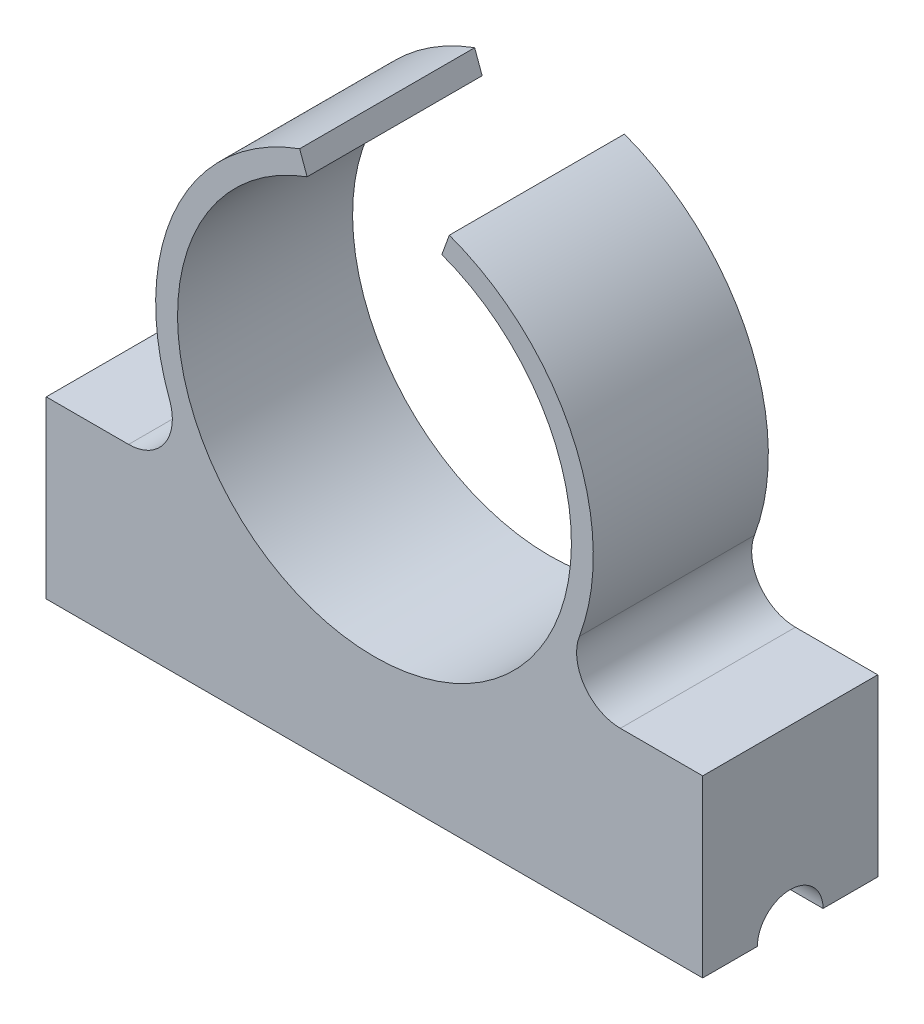
SolidWorks part; units mm, degrees
ref_plane "Front Plane" through (0, 0, 0) normal (0, 0, 1) x (1, 0, 0)
ref_plane "Top Plane" through (0, 0, 0) normal (0, 1, 0) x (1, 0, 0)
ref_plane "Right Plane" through (0, 0, 0) normal (1, 0, 0) x (0, 0, -1)
sketch "Sketch1" plane through (0, 0, 0) normal (0, 0, 1) x (1, 0, 0)
  line L0 (3.8901, 2.5) -> (15, 2.5)
  line L1 (-15, -2.5) -> (15, -2.5)
  line L2 (-15, -2.5) -> (-15, 2.5)
  line L3 (-15, 2.5) -> (-3.8901, 2.5)
  line L4 (15, -2.5) -> (15, 2.5)
  arc A3 (3.8901, 2.5) -> (-3.8901, 2.5) centre (0, 11.7123) ccw
  point P0 (0, 0)
extrude "Boss-Extrude1" add sketch "Sketch1" along normal blind 8
sketch "Sketch2" plane through (0, 0, 8) normal (0, 0, 1) x (1, 0, 0)
  circle A0 centre (0, 11.7123) radius 9
extrude "Cut-Extrude1" cut sketch "Sketch2" against normal blind 35
sketch "Sketch3" plane through (0, 0, 0) normal (0, 0, -1) x (-1, 0, 0)
  line L1 (-0.25, 22.4592) -> (0.25, 22.4592)
  line L2 (-0.25, 22.4592) -> (-0.25, 20.5838)
  line L3 (-0.25, 20.5838) -> (0.25, 20.5838)
  line L4 (0.25, 22.4592) -> (0.25, 20.5838)
  line L5 (-0.25, 22.4592) -> (0.25, 20.5838) construction
  line L6 (-0.25, 20.5838) -> (0.25, 22.4592) construction
  point P0 (0, 21.5215)
extrude "Cut-Extrude2" cut sketch "Sketch3" against normal blind 25
sketch "Sketch4" plane through (15, 0, 0) normal (1, 0, 0) x (0, 0, -1)
  line L0 (-8, -2.5) -> (0, -2.5) construction
  circle A0 centre (-4, -2.5) radius 1.5
extrude "Cut-Extrude3" cut sketch "Sketch4" against normal blind 110
sketch "Sketch6" plane through (0, 0, 8) normal (0, 0, 1) x (1, 0, 0)
  line L1 (-2.5, 26.3053) -> (2.5, 26.3053)
  line L2 (-2.5, 26.3053) -> (-2.5, 19.1581)
  line L3 (-2.5, 19.1581) -> (2.5, 19.1581)
  line L4 (2.5, 26.3053) -> (2.5, 19.1581)
  line L5 (-2.5, 26.3053) -> (2.5, 19.1581) construction
  line L6 (-2.5, 19.1581) -> (2.5, 26.3053) construction
  point P0 (0, 22.7317)
extrude "Cut-Extrude4" cut sketch "Sketch6" against normal blind 10
fillet "Fillet1" radius 0.5 2 edges at (3.8901, 2.5, 4) (-3.8901, 2.5, 4)
sketch "Sketch8" plane through (-15, 0, 0) normal (-1, 0, 0) x (0, 0, 1)
  line L5 (0, 2.5) -> (8, 2.5)
  line L6 (0, 2.5) -> (0, 5.5)
  line L7 (0, 5.5) -> (8, 5.5)
  line L8 (8, 2.5) -> (8, 5.5)
  point P0 (0, 2.5)
extrude "Boss-Extrude2" add sketch "Sketch8" against normal blind 30
sketch "Sketch9" plane through (0, 0, 0) normal (0, 0, -1) x (-1, 0, 0)
  circle A0 centre (0, 11.7123) radius 9
extrude "Cut-Extrude5" cut sketch "Sketch9" against normal blind 30
fillet "Fillet2" radius 2 2 edges at (7.8362, 5.5, 4) (-7.8362, 5.5, 4)
sketch "Sketch10" plane through (0, 0, 0) normal (0, 0, -1) x (-1, 0, 0)
  line L0 (0, 11.7123) -> (3.4202, 21.1093)
  line L2 (0, 11.7123) -> (-3.4202, 21.1093)
  arc A0 (9.3636, 8.2021) -> (2.5, 21.3948) centre (0, 11.7123) ccw construction
  arc A1 (-3.4202, 21.1093) -> (3.4202, 21.1093) centre (0, 21.1093) cw
extrude "Cut-Extrude7" cut sketch "Sketch10" against normal blind 30
